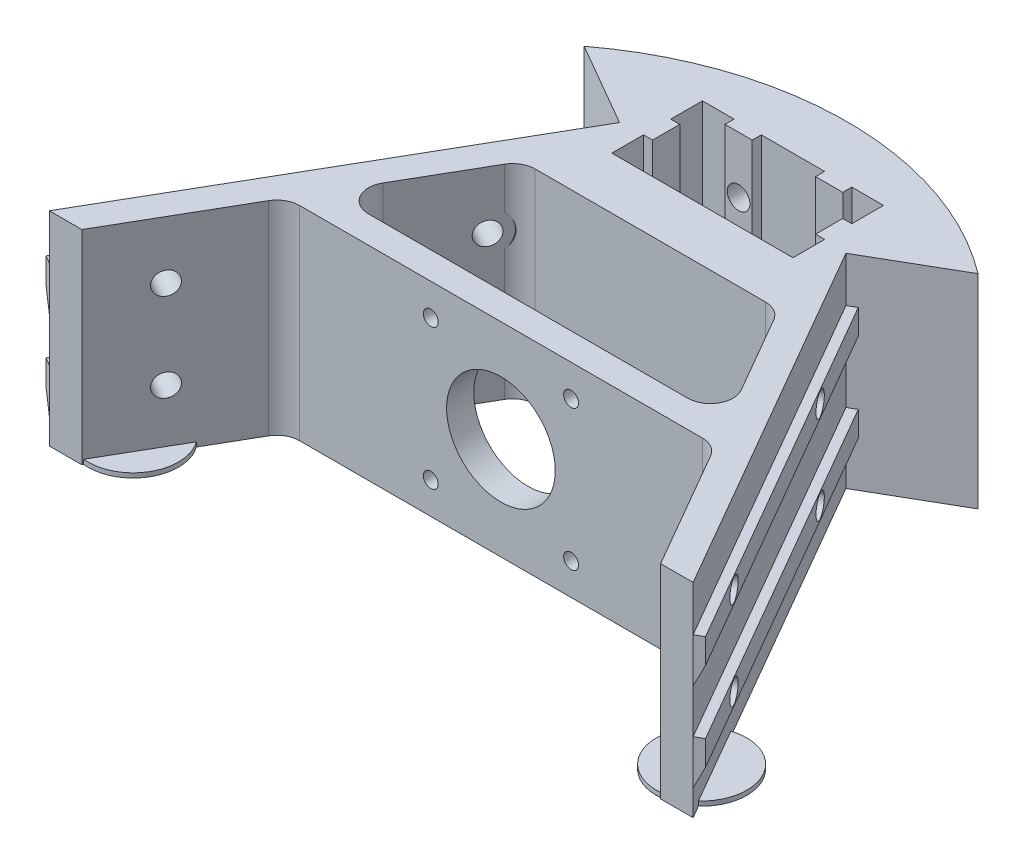
SolidWorks part; units mm, degrees
material "ABS"
ref_plane "Front Plane" through (0, 0, 0) normal (0, 0, 1) x (1, 0, 0)
ref_plane "Top Plane" through (0, 0, 0) normal (0, 1, 0) x (1, 0, 0)
ref_plane "Right Plane" through (0, 0, 0) normal (1, 0, 0) x (0, 0, -1)
sketch "Sketch1" plane through (0, 0, 0) normal (0, 1, 0) x (1, 0, 0)
  line L0 (0, -40) -> (0, 0) construction
  line L1 (-20, 20) -> (-13, 20)
  line L2 (-13, 20) -> (-13, 18)
  line L3 (-13, 18) -> (-7, 18)
  line L4 (-7, 18) -> (-7, 20)
  line L5 (-7, 20) -> (7, 20)
  line L6 (7, 20) -> (7, 18)
  line L7 (7, 18) -> (13, 18)
  line L8 (13, 18) -> (13, 20)
  line L9 (13, 20) -> (20, 20)
  line L10 (20, 20) -> (20, 13)
  line L11 (20, 13) -> (18, 13)
  line L12 (18, 13) -> (18, 7)
  line L13 (18, 7) -> (20, 7)
  line L14 (20, 7) -> (20, 0)
  line L15 (0, 20) -> (0, 0) construction
  line L16 (0, 0) -> (0, 50) construction
  line L17 (0, 50) -> (7.5492, 36.9243) construction
  line L18 (34.641, 70) -> (134.641, -103.2051) construction
  line L19 (20, 0) -> (-20, 0)
  line L20 (0, 50) -> (34.641, 70) construction
  line L21 (134.641, -103.2051) -> (100, -123.2051) construction
  line L22 (67.0736, -66.1749) -> (25, 6.6987)
  line L23 (25, 6.6987) -> (43.4956, 17.3771)
  line L24 (-20, 0) -> (-20, 7)
  line L25 (-20, 7) -> (-18, 7)
  line L26 (-18, 7) -> (-18, 13)
  line L27 (-18, 13) -> (-20, 13)
  line L28 (-20, 13) -> (-20, 20)
  line L29 (59.641, 26.6987) -> (134.641, -103.2051) construction
  line L30 (0, 50) -> (-7.0324, 37.8196) construction
  line L31 (0, 50) -> (-34.641, 70) construction
  line L32 (-34.641, 70) -> (-134.641, -103.2051) construction
  line L33 (-134.641, -103.2051) -> (-59.641, 26.6987) construction
  line L34 (-43.4956, 17.3771) -> (-25, 6.6987)
  line L35 (-25, 6.6987) -> (-67.0736, -66.1749)
  line L36 (-100, -123.2051) -> (-134.641, -103.2051) construction
  line L37 (0, -40) -> (0, -11.5) construction
  line L38 (-25.435, -11.5) -> (25.435, -11.5)
  line L39 (-35.25, -38.5) -> (35.25, -38.5)
  line L40 (-29.7652, -14) -> (-39.5801, -31)
  line L41 (29.7652, -14) -> (39.5801, -31)
  line L42 (-39.5801, -31) -> (-44.9691, -27.8887) construction
  line L43 (-39.5801, -31) -> (-47.1202, -44.0598) construction
  line L44 (-29.7652, -14) -> (-43.2264, -37.3156) construction
  line L45 (-35.1541, -10.8887) -> (-29.7652, -14) construction
  line L46 (-48.8177, -47) -> (-63.915, -73.1492)
  line L47 (-44.4876, -44.5) -> (44.4876, -44.5)
  line L48 (29.7652, -14) -> (39.5801, -31) construction
  line L49 (39.5801, -31) -> (46.43, -42.8643) construction
  line L50 (48.8177, -47) -> (63.915, -73.1492)
  line L51 (-67.0736, -66.1749) -> (-71.1002, -73.1492)
  line L52 (-71.1002, -73.1492) -> (-63.915, -73.1492)
  line L53 (67.0736, -66.1749) -> (71.1002, -73.1492)
  line L54 (71.1002, -73.1492) -> (63.915, -73.1492)
  arc A0 (63.915, -73.1492) -> (67.0736, -66.1749) centre (0, -40) ccw construction
  arc A1 (-25.435, -11.5) -> (-29.7652, -14) centre (-25.435, -16.5) ccw
  arc A2 (29.7652, -14) -> (25.435, -11.5) centre (25.435, -16.5) ccw
  arc A3 (35.25, -38.5) -> (39.5801, -31) centre (35.25, -33.5) ccw
  arc A4 (-39.5801, -31) -> (-35.25, -38.5) centre (-35.25, -33.5) ccw
  arc A5 (-44.4876, -44.5) -> (-48.8177, -47) centre (-44.4876, -49.5) ccw
  arc A6 (48.8177, -47) -> (44.4876, -44.5) centre (44.4876, -49.5) ccw
  arc A7 (-67.0736, -66.1749) -> (-63.915, -73.1492) centre (0, -40) ccw construction
  arc A8 (43.4956, 17.3771) -> (-43.4956, 17.3771) centre (0, -40) ccw
  dimension "D1" = 144
  dimension "D14" = 10
  dimension "D2" = 40
  dimension "D3" = 6
  dimension "D4" = 2
  dimension "D5" = 40
  dimension "D6" = 20
  dimension "D7" = 50
  dimension "D8" = 30
  dimension "D9" = 40
  dimension "D10" = 200
  dimension "D11" = 150
  dimension "D12" = 30
  dimension "D13" = 1.5
  dimension "D15" = 17
  dimension "D17" = 70.5
  dimension "D18" = 6
extrude "Boss-Extrude1" add sketch "Sketch1" along normal blind 45
sketch "Sketch2" plane through (0, 0, 44.5) normal (0, 0, 1) x (1, 0, 0)
  line L0 (0, 45) -> (0, 0) construction
  line L1 (-44.4876, 45) -> (44.4876, 45) construction
  line L2 (-15.5, 38) -> (0, 22.5) construction
  line L3 (0, 22.5) -> (15.5, 38) construction
  line L4 (0, 22.5) -> (15.5, 7) construction
  line L5 (-15.5, 7) -> (0, 22.5) construction
  circle A0 centre (0, 22.5) radius 12
  circle A1 centre (-15.5, 38) radius 1.65
  circle A2 centre (15.5, 38) radius 1.65
  circle A3 centre (15.5, 7) radius 1.65
  circle A4 centre (-15.5, 7) radius 1.65
  dimension "D1" = 24
  dimension "D2" = 3.3
  dimension "D3" = 31
  dimension "D4" = 31
extrude "Cut-Extrude1" cut sketch "Sketch2" against normal up to next
sketch "Sketch3" plane through (21.6506, 0, -12.5) normal (0.866, 0, -0.5) x (-0.5, 0, -0.866)
  line L0 (-98.8992, 35) -> (-6.6987, 35)
  line L1 (-98.8992, 45) -> (-98.8992, 0) construction
  line L2 (-6.6987, 45) -> (-6.6987, 0) construction
  line L3 (-6.6987, 35) -> (-6.6987, 29.5)
  line L4 (-6.6987, 29.5) -> (-98.8992, 29.5)
  line L5 (-98.8992, 29.5) -> (-98.8992, 35)
  line L6 (-98.8992, 15.5) -> (-6.6987, 15.5)
  line L7 (-6.6987, 15.5) -> (-6.6987, 10)
  line L8 (-6.6987, 10) -> (-98.8992, 10)
  line L9 (-98.8992, 10) -> (-98.8992, 15.5)
  line L10 (-98.8992, 22.5) -> (-6.6987, 22.5) construction
  line L11 (-6.6987, 45) -> (-6.6987, 0) construction
  line L12 (-98.8992, 22.5) -> (-98.8992, 29.5) construction
  line L13 (-98.8992, 22.5) -> (-98.8992, 15.5) construction
  dimension "D1" = 5.5
  dimension "D2" = 7
extrude "Boss-Extrude2" add sketch "Sketch3" along normal blind 2
sketch "Sketch4" plane through (23.3827, 0, -13.5) normal (0.866, 0, -0.5) x (-0.5, 0, -0.866)
  line L0 (-6.6987, 32.25) -> (-98.8992, 32.25) construction
  line L1 (-6.6987, 29.5) -> (-6.6987, 35) construction
  line L2 (-98.8992, 35) -> (-98.8992, 29.5) construction
  line L3 (-98.8992, 12.75) -> (-6.6987, 12.75) construction
  line L4 (-98.8992, 15.5) -> (-98.8992, 10) construction
  line L5 (-6.6987, 10) -> (-6.6987, 15.5) construction
  line L6 (-6.6987, 45) -> (-6.6987, 0) construction
  circle A0 centre (-29.6987, 32.25) radius 2.5
  circle A1 centre (-29.6987, 12.75) radius 2.5
  circle A2 centre (-81.6987, 12.75) radius 2.5
  circle A3 centre (-81.6987, 32.25) radius 2.5
  dimension "D1" = 5
  dimension "D3" = 75
  dimension "D2" = 23
extrude "Cut-Extrude2" cut sketch "Sketch4" against normal up to next
sketch "Sketch7" plane through (16.2617, 0, -9.3887) normal (-0.866, 0, 0.5) x (0.5, 0, 0.866)
  circle A0 centre (29.6987, 32.25) radius 4.5
  circle A1 centre (29.6987, 12.75) radius 4.5
  dimension "D1" = 9
extrude "Cut-Extrude6" cut sketch "Sketch7" along normal up to next
sketch "Sketch5" plane through (0, 0, -18) normal (0, 0, 1) x (1, 0, 0)
  line L0 (7, 22.5) -> (13, 22.5) construction
  line L1 (7, 45) -> (7, 0) construction
  line L2 (13, 45) -> (13, 0) construction
  line L3 (10, 22.5) -> (10, 32.5) construction
  line L4 (10, 22.5) -> (10, 12.5) construction
  circle A0 centre (10, 32.5) radius 2.5
  circle A1 centre (10, 12.5) radius 2.5
  dimension "D1" = 20
  dimension "D2" = 5
extrude "Cut-Extrude3" cut sketch "Sketch5" against normal up to next
sketch "Sketch6" plane through (0, 0, -18) normal (0, 0, 1) x (1, 0, 0)
  circle A0 centre (10, 32.5) radius 4.25
  circle A1 centre (10, 12.5) radius 4.25
  dimension "D1" = 8.5
extrude "Cut-Extrude5" cut sketch "Sketch6" along normal blind 1.7 from offset 14 offset against normal yes
mirror "Mirror1" about plane through (0, 0, 0) normal (1, 0, 0) of "Cut-Extrude6", "Cut-Extrude5", "Cut-Extrude3", "Cut-Extrude2", "Boss-Extrude2"
sketch "Sketch8" plane through (0, 0, 0) normal (0, 1, 0) x (1, 0, 0)
  line L0 (59.2113, -65.0022) -> (66.3323, -60.8909) construction
  line L1 (48.8177, -47) -> (63.915, -73.1492) construction
  line L2 (26.7321, 7.6987) -> (72.8323, -72.1492) construction
  line L3 (72.8323, -72.1492) -> (71.1002, -73.1492) construction
  line L4 (-59.2113, -65.0022) -> (-66.3323, -60.8909) construction
  line L5 (-63.915, -73.1492) -> (-48.8177, -47) construction
  line L6 (-26.7321, 7.6987) -> (-72.8323, -72.1492) construction
  circle A0 centre (62.7718, -62.9466) radius 10
  circle A1 centre (-62.7718, -62.9466) radius 10
  dimension "D1" = 20
  dimension "D2" = 13
extrude "Boss-Extrude3" add sketch "Sketch8" along normal blind 1
sketch "Sketch10" plane through (49.4496, 0, 85.6492) normal (0.5, 0, 0.866) x (0.866, 0, -0.5)
  line L1 (25, 29.5) -> (27, 29.5)
  line L2 (27, 29.5) -> (25, 25.211)
  line L3 (25, 29.5) -> (25, 15.5) construction
  line L4 (25, 25.211) -> (25, 29.5)
  line L5 (25, 10) -> (27, 10)
  line L6 (27, 10) -> (25, 5.711)
  line L7 (25, 10) -> (25, 0) construction
  line L8 (25, 5.711) -> (25, 10)
  dimension "D1" = 65
extrude "Boss-Extrude4" add sketch "Sketch10" against normal blind 0.7
pattern_linear "LPattern1" count 46 spacing 2 along (-0.5, 0, -0.866) of "Boss-Extrude4"
sketch "Sketch11" plane through (-49.4496, 0, 85.6492) normal (-0.5, 0, 0.866) x (0.866, 0, 0.5)
  line L0 (-25, 29.5) -> (-27, 29.5)
  line L1 (-27, 29.5) -> (-25, 25.211)
  line L2 (-25, 29.5) -> (-25, 15.5) construction
  line L3 (-25, 25.211) -> (-25, 29.5)
  line L4 (-25, 10) -> (-27, 10)
  line L5 (-27, 10) -> (-25, 5.711)
  line L6 (-25, 10) -> (-25, 0) construction
  line L7 (-25, 5.711) -> (-25, 10)
  dimension "D1" = 65
extrude "Boss-Extrude5" add sketch "Sketch11" against normal blind 0.7
pattern_linear "LPattern2" count 46 spacing 2 along (0.5, 0, -0.866) of "Boss-Extrude5"
equation "\"D12@Sketch1\"=\"D8@Sketch1\""
equation "\"D4@Sketch2\"=\"D3@Sketch2\""
equation "\"D2@Sketch3\"=(20-6)/2"
